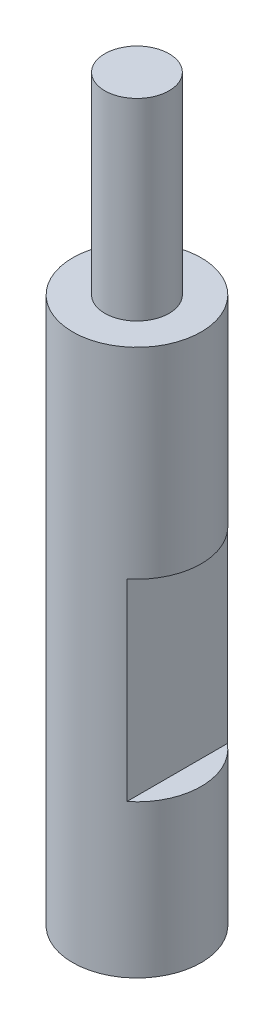
SolidWorks part; units mm, degrees
ref_plane "Front Plane" through (0, 0, 0) normal (0, 0, 1) x (1, 0, 0)
ref_plane "Top Plane" through (0, 0, 0) normal (0, 1, 0) x (1, 0, 0)
ref_plane "Right Plane" through (0, 0, 0) normal (1, 0, 0) x (0, 0, -1)
sketch "Sketch1" plane through (0, 0, 0) normal (0, 1, 0) x (1, 0, 0)
  circle A0 centre (0, 0) radius 4
  dimension "D1" = 8
extrude "Boss-Extrude1" add sketch "Sketch1" along normal blind 34
sketch "Sketch2" plane through (0, 34, 0) normal (0, 1, 0) x (1, 0, 0)
  circle A0 centre (0, 0) radius 2
  dimension "D1" = 4
extrude "Boss-Extrude2" add sketch "Sketch2" along normal blind 12
sketch "Sketch3" plane through (0, 0, 0) normal (0, 0, 1) x (1, 0, 0)
  line L0 (-4, 0) -> (4, 0) construction
  line L1 (4, 9.5) -> (2.5, 9.5)
  line L2 (4, 9.5) -> (4, 21.5)
  line L3 (4, 21.5) -> (2.5, 21.5)
  line L4 (2.5, 9.5) -> (2.5, 21.5)
  line L5 (4, 9.5) -> (2.5, 21.5) construction
  line L6 (4, 21.5) -> (2.5, 9.5) construction
  line L7 (4, 0) -> (4, 34) construction
  point P0 (3.25, 15.5)
  dimension "D1" = 12
  dimension "D2" = 9.5
  dimension "D3" = 1.5
extrude "Cut-Extrude1" cut sketch "Sketch3" against normal through all both and the other way through all
hole_wizard "M3 Tapped Hole1" positions "Sketch5" profile "Sketch6" tap size "M3" standard "ISO"
sketch "Sketch5" plane through (0, 0, 0) normal (0, -1, 0) x (-1, 0, 0)
  point P0 (0, 0)
sketch "Sketch6" plane through (0, 0, 0) normal (1, 0, 0) x (0, 0, -1)
  line L0 (0, 0) -> (0, 14.7511)
  line L1 (0, 14.7511) -> (1.25, 14)
  line L2 (1.25, 14) -> (1.25, 0.275)
  line L3 (1.25, 0.275) -> (1.525, 0)
  line L5 (1.525, 0) -> (0, 0)
  line L6 (-1.25, 0.275) -> (-1.525, 0) construction
  line L10 (0, 14.7511) -> (-1.25, 14) construction
  line L11 (0, -6.35) -> (0, 107.95) construction
  dimension "Tap Drill Dia." = 2.5
  dimension "Tap Drill Depth" = 14
  dimension "Near C'Sink Dia." = 3.05
  dimension "Near C'Sink Angle" = 90
  dimension "Drill Angle" = 118
cosmetic thread "Hole Thread1" parameters "D1"=2, "D2"=3
sketch "Sketch7" plane through (0, 0, 0) normal (1, 0, 0) x (0, 0, -1)
  line L0 (-4, 0) -> (4, 0) construction
  circle A0 centre (0, 11.5) radius 2
  dimension "D1" = 4
  dimension "D2" = 11.5
extrude "Cut-Extrude2" cut sketch "Sketch7" against normal blind 12
